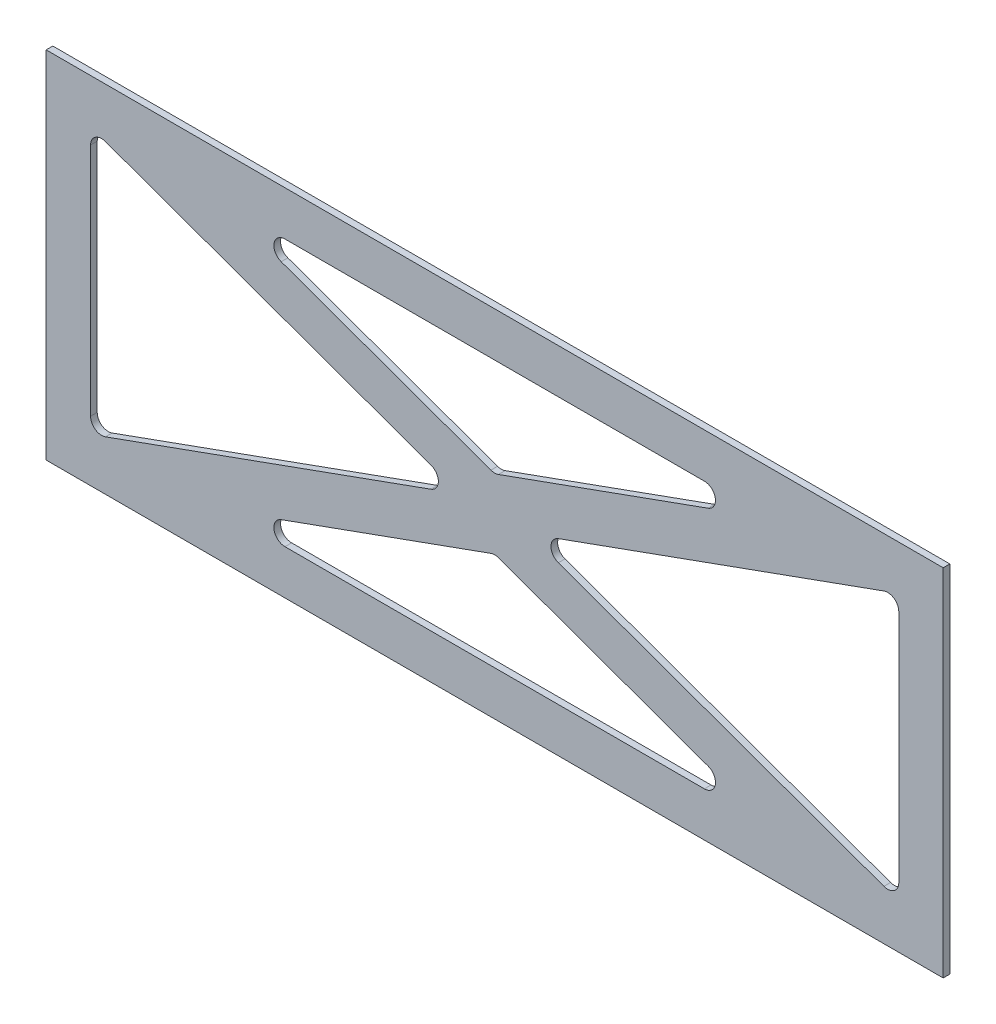
SolidWorks part; units mm, degrees
material "birch 3mm plywood"
ref_plane "Front Plane" through (0, 0, 0) normal (0, 0, 1) x (1, 0, 0)
ref_plane "Top Plane" through (0, 0, 0) normal (0, 1, 0) x (1, 0, 0)
ref_plane "Right Plane" through (0, 0, 0) normal (1, 0, 0) x (0, 0, -1)
sketch "Sketch1" plane through (0, 0, 152) normal (0, 0, 1) x (1, 0, 0)
  line L1 (-67.5, -5.9413) -> (336.5, -5.9413)
  line L2 (-67.5, -5.9413) -> (-67.5, -165.9413)
  line L3 (-67.5, -165.9413) -> (336.5, -165.9413)
  line L4 (336.5, -5.9413) -> (336.5, -165.9413)
  line L6 (-47.5, -138.823) -> (-47.5, -33.0597)
  line L7 (-40.8038, -28.3562) -> (105.832, -81.2379)
  line L9 (-65.5, -84) -> (-65.5, 66) construction
  line L12 (334.5, -160.9413) -> (-65.5, -160.9413) construction
  line L13 (334.5, -10.9413) -> (334.5, -160.9413) construction
  line L14 (-65.5, -160.9413) -> (-65.5, -10.9413) construction
  line L15 (-65.5, -10.9413) -> (334.5, -10.9413) construction
  line L18 (228.9427, -25.9413) -> (40.0573, -25.9413)
  line L19 (105.832, -90.6448) -> (-40.8038, -143.5265)
  line L20 (38.3611, -35.6448) -> (132.8038, -69.7039)
  line L21 (136.1962, -69.7039) -> (230.6389, -35.6448)
  line L22 (334.5, -49) -> (334.5, 31) construction
  line L23 (309.8038, -28.3562) -> (163.168, -81.2379)
  line L24 (316.5, -138.823) -> (316.5, -33.0597)
  line L25 (163.168, -90.6448) -> (309.8038, -143.5265)
  line L26 (-65.5, -85.9413) -> (334.5, -85.9413) construction
  line L27 (38.3611, -136.2379) -> (132.8038, -102.1787)
  line L28 (228.9427, -145.9413) -> (40.0573, -145.9413)
  line L29 (136.1962, -102.1787) -> (230.6389, -136.2379)
  line L30 (134.5, -70.3157) -> (134.5, -101.567) construction
  line L31 (118.8743, -85.9413) -> (150.1257, -85.9413) construction
  line L32 (134.5, -70.3157) -> (134.5, -101.567) construction
  line L41 (234.5, -160.9413) -> (-65.5, -160.9413) construction
  line L42 (234.5, -10.9413) -> (-65.5, -10.9413) construction
  arc A0 (-40.8038, -143.5265) -> (-47.5, -138.823) centre (-42.5, -138.823) cw
  arc A1 (105.832, -90.6448) -> (105.832, -81.2379) centre (104.1358, -85.9413) ccw
  arc A2 (-40.8038, -28.3562) -> (-47.5, -33.0597) centre (-42.5, -33.0597) ccw
  arc A3 (230.6389, -136.2379) -> (228.9427, -145.9413) centre (228.9427, -140.9413) cw
  arc A4 (38.3611, -136.2379) -> (40.0573, -145.9413) centre (40.0573, -140.9413) ccw
  arc A5 (132.8038, -102.1787) -> (136.1962, -102.1787) centre (134.5, -106.8822) cw
  arc A6 (163.168, -81.2379) -> (163.168, -90.6448) centre (164.8642, -85.9413) ccw
  arc A7 (309.8038, -143.5265) -> (316.5, -138.823) centre (311.5, -138.823) ccw
  arc A8 (316.5, -33.0597) -> (309.8038, -28.3562) centre (311.5, -33.0597) ccw
  arc A9 (38.3611, -35.6448) -> (40.0573, -25.9413) centre (40.0573, -30.9413) cw
  arc A10 (230.6389, -35.6448) -> (228.9427, -25.9413) centre (228.9427, -30.9413) ccw
  arc A11 (136.1962, -69.7039) -> (132.8038, -69.7039) centre (134.5, -65.0005) cw
  point P14 (134.5, -85.9413)
  point P15 (134.5, -85.9413)
  point P32 (-47.5, -25.9413)
  point P35 (257.5458, -145.9413)
  point P38 (11.4542, -145.9413)
  point P51 (11.4542, -25.9413)
  point P54 (257.5458, -25.9413)
  dimension "D9" = 5
  dimension "D10" = 5
  dimension "D1" = 2
  dimension "D2" = 2
  dimension "D3" = 5
  dimension "D4" = 5
  dimension "D5" = 20
  dimension "D6" = 20
  dimension "D7" = 20
  dimension "D8" = 20
  dimension "D11" = 20
extrude "Boss-Extrude1" add sketch "Sketch1" along normal blind 3
